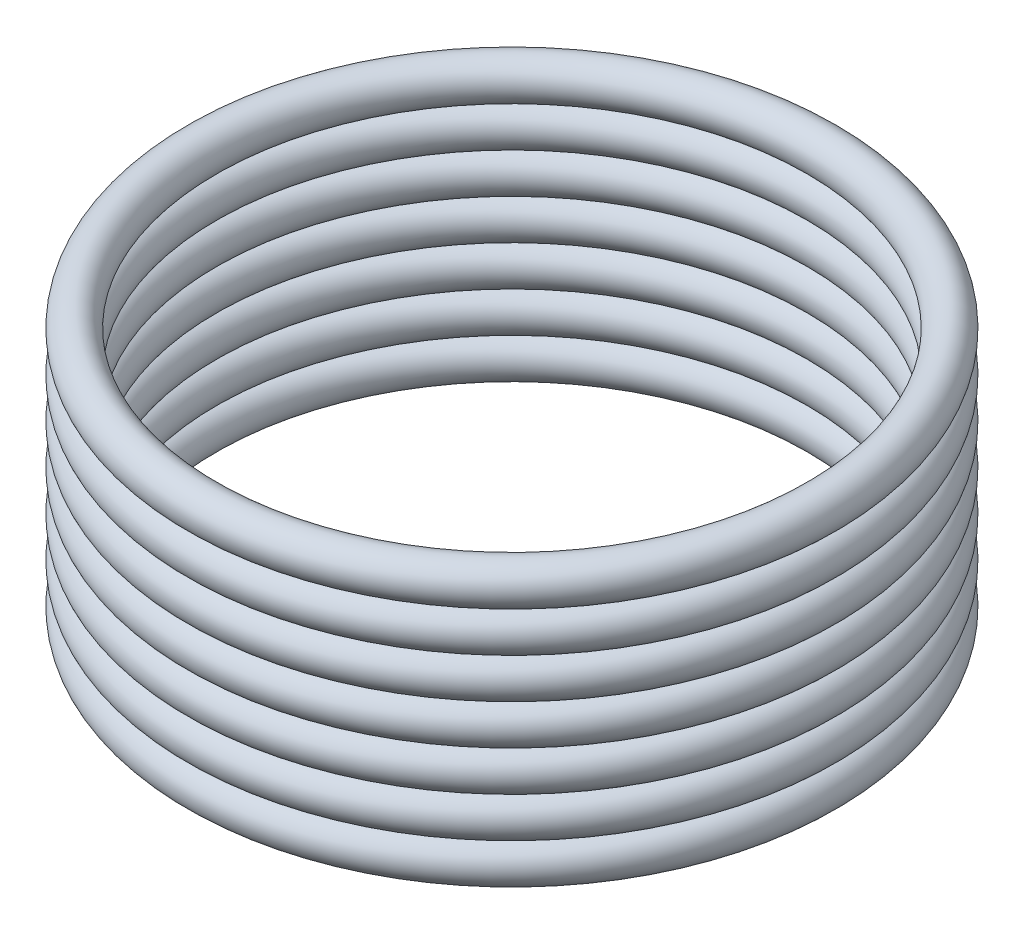
SolidWorks part; units mm, degrees
ref_plane "前视基准面" through (0, 0, 0) normal (0, 0, 1) x (1, 0, 0)
ref_plane "上视基准面" through (0, 0, 0) normal (0, 1, 0) x (1, 0, 0)
ref_plane "右视基准面" through (0, 0, 0) normal (1, 0, 0) x (0, 0, -1)
other "Configuration Table"
sketch "草图1" plane through (0, 0, 0) normal (0, 0, 1) x (1, 0, 0)
  line L0 (0, 0) -> (108, 0) construction
  line L1 (115, 0) -> (115, 29.0176) construction
  line L2 (0, 0) -> (0, 48.7359) construction
  circle A0 centre (108, 0) radius 7
  dimension "D1" = 14
  dimension "D2" = 115
revolve "旋转1" add sketch "草图1" angle 360 about L2
sketch "草图2" plane through (0, 0, 0) normal (0, 0, 1) x (1, 0, 0)
  line L0 (0, 0) -> (0, 14) construction
  line L1 (0, 14) -> (108, 14) construction
  circle A0 centre (108, 14) radius 7
  dimension "D2" = 14
  dimension "D1" = 108
  dimension "D3" = 14
revolve "旋转2" add sketch "草图2" angle 360 about L0
sketch "草图3" plane through (0, 0, 0) normal (0, 0, 1) x (1, 0, 0)
  line L0 (0, 0) -> (0, 28) construction
  line L1 (0, 28) -> (108, 28) construction
  circle A0 centre (108, 28) radius 7
  dimension "D3" = 14
  dimension "D1" = 108
  dimension "D2" = 28
revolve "旋转3" add sketch "草图3" angle 360 about L0
sketch "草图4" plane through (0, 0, 0) normal (0, 0, 1) x (1, 0, 0)
  line L0 (0, 0) -> (0, 42) construction
  line L1 (0, 42) -> (108, 42) construction
  circle A0 centre (108, 42) radius 7
  dimension "D1" = 14
  dimension "D2" = 108
  dimension "D3" = 42
revolve "旋转4" add sketch "草图4" angle 360 about L0
sketch "草图5" plane through (0, 0, 0) normal (0, 0, 1) x (1, 0, 0)
  line L0 (0, 0) -> (0, 56) construction
  line L1 (0, 56) -> (108, 56) construction
  circle A0 centre (108, 56) radius 7
  dimension "D1" = 14
  dimension "D2" = 108
  dimension "D3" = 56
revolve "旋转5" add sketch "草图5" angle 360 about L0
sketch "草图6" plane through (0, 0, 0) normal (0, 0, 1) x (1, 0, 0)
  line L0 (0, 0) -> (0, 70) construction
  line L1 (0, 70) -> (108, 70) construction
  circle A0 centre (108, 70) radius 7
  dimension "D1" = 14
  dimension "D2" = 108
  dimension "D3" = 70
revolve "旋转6" add sketch "草图6" angle 360 about L0
sketch "草图7" plane through (0, 0, 0) normal (0, 0, 1) x (1, 0, 0)
  line L0 (0, 0) -> (0, 84) construction
  line L1 (0, 84) -> (108, 84) construction
  circle A0 centre (108, 84) radius 7
  dimension "D1" = 14
  dimension "D2" = 108
  dimension "D3" = 84
revolve "旋转7" add sketch "草图7" angle 360 about L0
